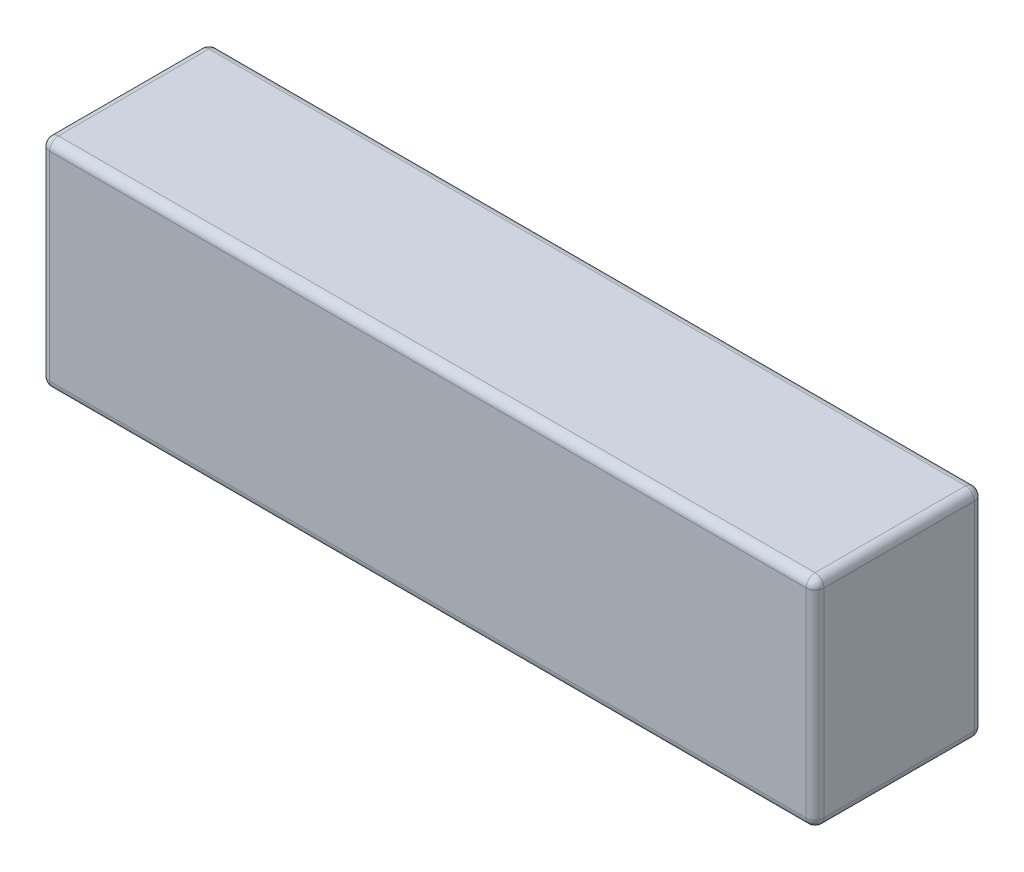
SolidWorks part; units mm, degrees
ref_plane "Front Plane" through (0, 0, 0) normal (0, 0, 1) x (1, 0, 0)
ref_plane "Top Plane" through (0, 0, 0) normal (0, 1, 0) x (1, 0, 0)
ref_plane "Right Plane" through (0, 0, 0) normal (1, 0, 0) x (0, 0, -1)
sketch "Sketch1" plane through (0, 0, 0) normal (0, 1, 0) x (1, 0, 0)
  line L1 (0, 0) -> (175, 0)
  line L2 (0, 0) -> (0, 38)
  line L3 (0, 38) -> (175, 38)
  line L4 (175, 0) -> (175, 38)
  dimension "D1" = 175
  dimension "D2" = 38
extrude "Boss-Extrude1" add sketch "Sketch1" along normal blind 49
fillet "Fillet1" radius 2 12 edges at (0, 24.5, 0) (175, 24.5, 0) (87.5, 0, 0) (175, 0, -19) (0, 0, -19) (175, 49, -19) (87.5, 49, 0) (0, 49, -19) (175, 24.5, -38) (87.5, 49, -38) (0, 24.5, -38) (87.5, 0, -38)
